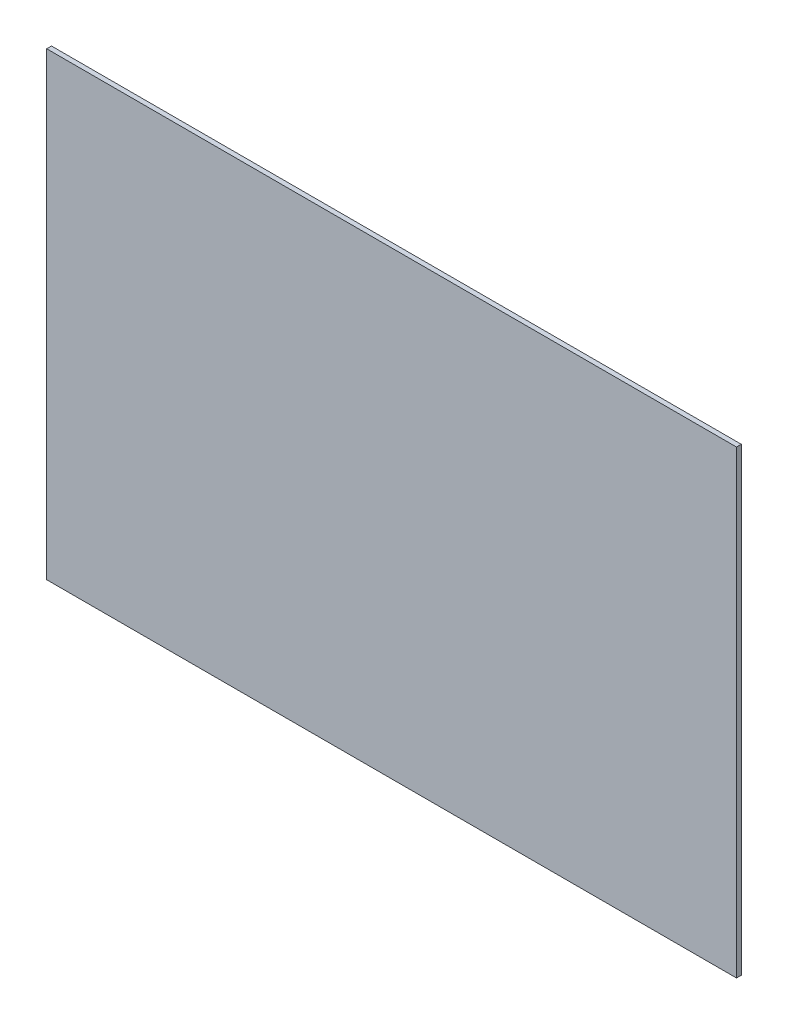
SolidWorks part; units mm, degrees
ref_plane "Front Plane" through (0, 0, 0) normal (0, 0, 1) x (1, 0, 0)
ref_plane "Top Plane" through (0, 0, 0) normal (0, 1, 0) x (1, 0, 0)
ref_plane "Right Plane" through (0, 0, 0) normal (1, 0, 0) x (0, 0, -1)
sketch "Sketch1" plane through (0, 0, 0) normal (0, 0, 1) x (1, 0, 0)
  line L1 (-257.4871, 166.5463) -> (199.7129, 166.5463)
  line L2 (-257.4871, 166.5463) -> (-257.4871, -138.2537)
  line L3 (-257.4871, -138.2537) -> (199.7129, -138.2537)
  line L4 (199.7129, 166.5463) -> (199.7129, -138.2537)
  dimension "D1" = 457.2
  dimension "D2" = 304.8
extrude "Boss-Extrude1" add sketch "Sketch1" along normal blind 3.175
